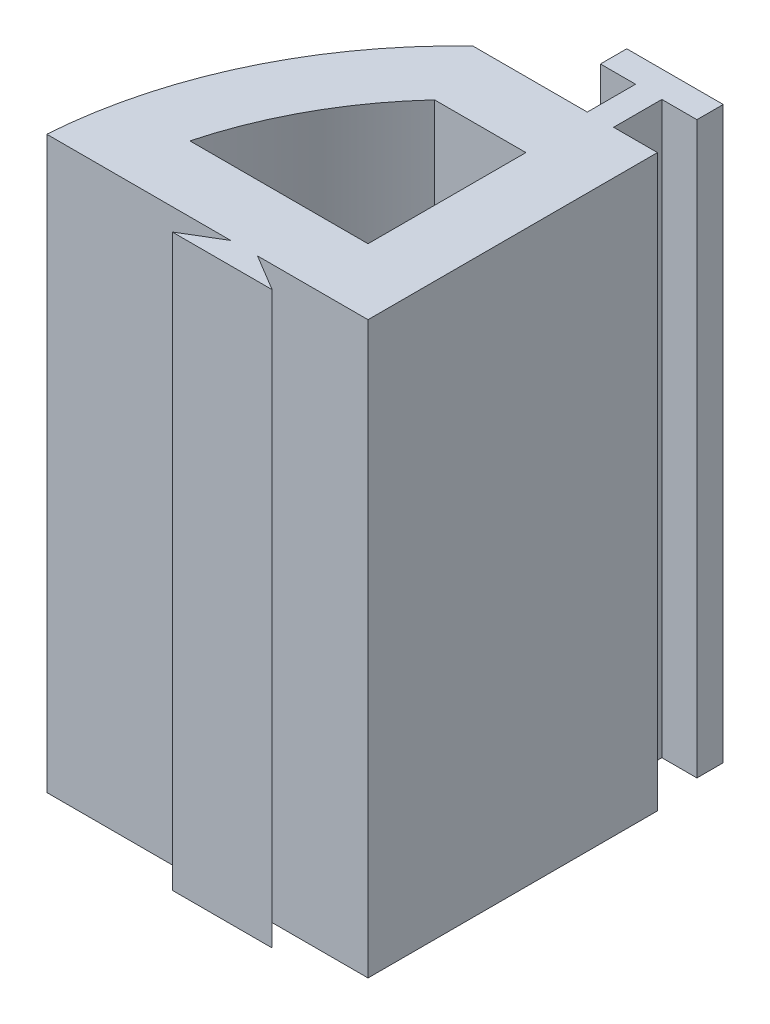
SolidWorks part; units mm, degrees
ref_plane "Front Plane" through (0, 0, 0) normal (0, 0, 1) x (1, 0, 0)
ref_plane "Top Plane" through (0, 0, 0) normal (0, 1, 0) x (1, 0, 0)
ref_plane "Right Plane" through (0, 0, 0) normal (1, 0, 0) x (0, 0, -1)
sketch "Sketch1" plane through (0, 0, 0) normal (0, 1, 0) x (1, 0, 0)
  line L0 (-0.45, 7.3) -> (-0.45, 0.7)
  line L1 (0, 10.25) -> (0, -10.25) construction
  line L2 (0, 0) -> (-11.05, 0) construction
  line L3 (-0.45, 0.7) -> (-10.0378, 0.7)
  line L4 (-0.25, 0) -> (-0.25, -10.247) construction
  line L5 (-0.25, -10.247) -> (-0.25, 10.247) construction
  line L6 (0.25, -10.247) -> (0.25, 10.247) construction
  line L7 (-0.25, -7.5) -> (-6.9866, -7.5) construction
  line L8 (-6.9866, -7.5) -> (6.9866, -7.5) construction
  line L9 (-6.9866, 7.5) -> (6.9866, 7.5) construction
  line L10 (-10.0378, 0.7) -> (-10.0378, 5.7041)
  line L11 (-10.0378, 5.7041) -> (-8.9399, 7.3)
  line L12 (-10.2378, 0.5) -> (10.2378, 0.5) construction
  line L13 (10.2378, -7.5) -> (6.9866, -7.5) construction
  line L14 (6.9866, -7.5) -> (10.2378, -7.5) construction
  line L15 (10.2378, -7.5) -> (10.2378, -0.5) construction
  line L26 (-0.25, 0.5) -> (-10.2378, 0.5)
  line L27 (-0.25, 7.5) -> (-0.25, 0.5)
  line L28 (-9.045, 7.5) -> (-0.25, 7.5)
  line L29 (-10.2378, 5.7663) -> (-9.045, 7.5)
  line L30 (-10.2378, 0.5) -> (-10.2378, 5.7663)
  line L36 (-0.25, -7.5) -> (-0.25, -8.2)
  line L37 (-0.25, -8.2) -> (0.25, -8.2)
  line L38 (0.25, -8.2) -> (0.25, -7.5)
  line L39 (-0.25, 7.5) -> (-0.25, 8.2)
  line L40 (-0.25, 8.2) -> (0.25, 8.2)
  line L41 (0.25, 8.2) -> (0.25, 7.5)
  line L42 (-8.9399, 7.3) -> (-0.45, 7.3)
  line L43 (-4.3, 7.5) -> (-4.3, 8.4)
  line L44 (-4.3, 8.4) -> (-5.1, 8.4)
  line L45 (-5.1, 8.4) -> (-5.1, 9)
  line L46 (-5.1, 9) -> (-2.9, 9)
  line L47 (-2.9, 9) -> (-2.9, 8.4)
  line L48 (-2.9, 8.4) -> (-3.7, 8.4)
  line L49 (-3.7, 8.4) -> (-3.7, 7.5)
  line L50 (-4.3, 7.5) -> (-4.3, 7.3)
  line L51 (-3.7, 7.5) -> (-3.7, 7.3)
  line L52 (-2.7, 7.5) -> (-2.7, 0.5)
  line L53 (-4.025, 0) -> (-7.025, 0)
  line L54 (0, 0.4) -> (-11.05, 0.4) construction
  line L55 (-4.025, 0.1) -> (-7.025, 0.1)
  line L56 (-5.2, 8.3) -> (-5.2, 9.1)
  line L57 (-4.4, 8.3) -> (-5.2, 8.3)
  line L58 (-4.4, 7.5) -> (-4.4, 8.3)
  line L59 (-3.6, 8.3) -> (-3.6, 7.5)
  line L60 (-2.8, 8.3) -> (-3.6, 8.3)
  line L61 (-2.8, 9.1) -> (-2.8, 8.3)
  line L62 (-5.2, 9.1) -> (-2.8, 9.1)
  line L63 (-7.025, 0.1) -> (-6.525, 0.4)
  line L64 (-5.525, 0) -> (-5.525, 0.4) construction
  line L65 (-4.025, 0.1) -> (-4.525, 0.4)
  line L66 (-6.525, 0.4) -> (-6.025, 0.7)
  line L67 (-4.525, 0.4) -> (-5.025, 0.7)
  line L68 (-4.5764, 0.3143) -> (-5.0764, 0.6143)
  line L69 (-4.386, 0.2) -> (-4.5764, 0.3143)
  line L70 (-4.386, 0.2) -> (-6.664, 0.2)
  line L71 (-6.664, 0.2) -> (-6.4736, 0.3143)
  line L72 (-6.4736, 0.3143) -> (-5.9736, 0.6143)
  line L73 (-5.9736, 0.6143) -> (-5.8306, 0.7)
  line L74 (10.2378, 0.5) -> (10.55, 0.5)
  line L75 (10.55, 0) -> (10.55, -0.5)
  line L76 (10.55, -0.5) -> (10.2378, -0.5)
  line L77 (10.55, 0.5) -> (10.55, 0)
  line L102 (-2.5, 7.5) -> (-2.5, 0.5)
  line L103 (-5.0764, 0.6143) -> (-5.2194, 0.7)
  circle A3 centre (0, 0) radius 10.05
  circle A4 centre (0, 0) radius 10.25
  point P3 (-0.25, 0)
  point P13 (-0.25, -7.5)
  point P20 (-0.25, -0.5)
  point P21 (-5.525, 0)
  point P28 (0, -9.7)
  point P49 (-0.25, -8.2)
  point P53 (-5.8308, 0.6313)
  point P55 (-4.025, 0)
  point P56 (-5.525, 0)
  point P58 (4.4, -7.5)
  point P59 (4.4, -7.5)
  point P61 (-6.525, 0.4)
  point P78 (-6.525, 0.1)
  point P93 (-5.525, 0.2)
  point P104 (-10.55, 0)
  point P105 (10.55, -0.25)
  point P125 (-2.5, 7.5)
  dimension "D1" = 0.2
  dimension "D2" = 0.1
  dimension "D4" = 0.4
  dimension "D3" = 0.2
  dimension "D5" = 0.1
  dimension "D6" = 0.1
extrude "Boss-Extrude1" add sketch "Sketch1" along normal blind 13 contours L42 A3 L3 L52 | L68 L103 L3 L73 L72 L26 | L72 L71 L70 L69 L68 L26 | L51 L28 L50 L42 | L46 A3 L45 L44 L43 L28 L49 L48 L47 | L46 A4 L45 A3 | A4 L46 L45
sketch "Sketch2" plane through (0, 13, 0) normal (0, 1, 0) x (1, 0, 0)
  line L0 (-2.7, 0.7) -> (-2.7, 7.3)
  line L1 (-2.7, 7.3) -> (-6.9074, 7.3)
  line L2 (-2.7, 0.7) -> (-10.0256, 0.7)
  line L18 (-4.2, 7.2) -> (-3.8, 7.2)
  line L19 (-4.2, 2.2) -> (-4.2, 5.8)
  line L20 (-4.2, 5.8) -> (-4.2, 5.8)
  line L21 (-4.2, 5.8) -> (-4.2, 5.8)
  line L22 (-4.2, 5.8) -> (-6.2819, 5.8)
  line L23 (-8.2621, 2.2) -> (-4.2, 2.2)
  line L24 (-2.7, -0.7) -> (-10.0256, -0.7)
  line L33 (-4.2, 7.2) -> (-6.8675, 7.2)
  line L34 (-9.9178, 0.8) -> (-2.8, 0.8)
  line L35 (-2.8, 0.8) -> (-2.8, 7.2)
  line L36 (-2.8, 7.2) -> (-3.8, 7.2)
  line L37 (-3.8, 7.2) -> (-3.8, 8.5)
  line L38 (-3.8, 8.5) -> (-3, 8.5)
  line L39 (-3, 8.5) -> (-3, 8.9)
  line L40 (-3, 8.9) -> (-5, 8.9)
  line L41 (-5, 8.9) -> (-5, 8.5)
  line L42 (-5, 8.5) -> (-4.2, 8.5)
  line L43 (-4.2, 8.5) -> (-4.2, 7.2)
  line L44 (-4.2, 7.2) -> (-6.8675, 7.2)
  line L45 (-9.9178, 0.8) -> (-2.8, 0.8)
  line L46 (-2.8, 0.8) -> (-2.8, 7.2)
  line L47 (-2.8, 7.2) -> (-3.8, 7.2)
  line L48 (-3.8, 7.2) -> (-3.8, 8.5)
  line L49 (-3.8, 8.5) -> (-3, 8.5)
  line L50 (-3, 8.5) -> (-3, 8.9)
  line L51 (-3, 8.9) -> (-5, 8.9)
  line L52 (-5, 8.9) -> (-5, 8.5)
  line L53 (-5, 8.5) -> (-4.2, 8.5)
  line L54 (-4.2, 8.5) -> (-4.2, 7.2)
  arc A1 (-6.2819, 5.8) -> (-8.2621, 2.2) centre (0, 0) ccw
  arc A2 (-6.8675, 7.2) -> (-9.9178, 0.8) centre (0, 0) ccw
  arc A3 (-6.8675, 7.2) -> (-9.9178, 0.8) centre (0, 0) ccw
  dimension "D1" = 0.1
  dimension "D2" = 1.4
extrude "Cut-Extrude1" cut sketch "Sketch2" against normal through all contours L22 A1 L23 L19
